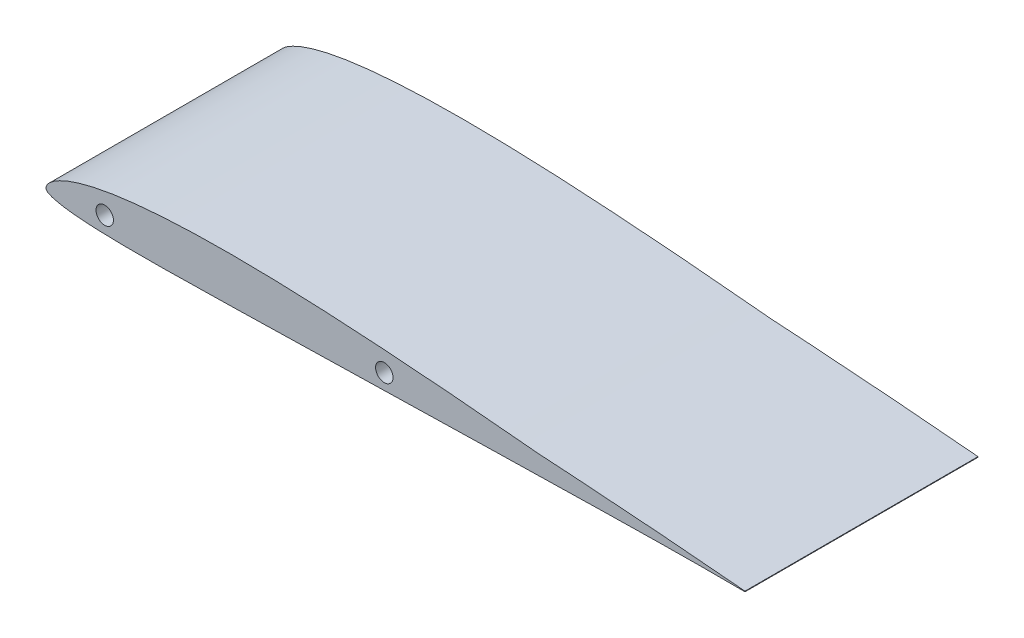
SolidWorks part; units mm, degrees
ref_plane "Front Plane" through (0, 0, 0) normal (0, 0, 1) x (1, 0, 0)
ref_plane "Top Plane" through (0, 0, 0) normal (0, 1, 0) x (1, 0, 0)
ref_plane "Right Plane" through (0, 0, 0) normal (1, 0, 0) x (0, 0, -1)
curve "Curve1"
  spline degree 3 poles (25.4, 0.0107, 0) (25.3506, 0.0152, 0) (25.2009, 0.0289, 0) (24.9376, 0.0531, 0) (24.6076, 0.082, 0) (24.2616, 0.1124, 0) (23.9125, 0.1431, 0) (23.5625, 0.1725, 0) (23.212, 0.2019, 0) (22.8613, 0.2307, 0) (22.5105, 0.2591, 0) (22.1596, 0.2869, 0) (21.8089, 0.314, 0) (21.4582, 0.3409, 0) (21.1077, 0.367, 0) (20.7573, 0.3928, 0) (20.407, 0.4182, 0) (20.0568, 0.4428, 0) (19.7068, 0.4673, 0) (19.3568, 0.4911, 0) (19.0069, 0.5145, 0) (18.6571, 0.5374, 0) (18.3335, 0.5583, 0) (18.0818, 0.5739, 0) (17.9246, 0.5843, 0) (17.8356, 0.5888, 0) (17.7472, 0.5983, 0) (17.5613, 0.6156, 0) (17.278, 0.6431, 0) (16.98, 0.6709, 0) (16.7137, 0.6956, 0) (16.4751, 0.7176, 0) (16.176, 0.7447, 0) (15.8267, 0.776, 0) (15.4701, 0.8073, 0) (15.1145, 0.838, 0) (14.7793, 0.8663, 0) (14.4495, 0.8936, 0) (14.1621, 0.9169, 0) (13.925, 0.9358, 0) (13.6642, 0.9563, 0) (13.3619, 0.9794, 0) (13.0103, 1.0056, 0) (12.659, 1.031, 0) (12.3077, 1.0554, 0) (11.9565, 1.0789, 0) (11.6054, 1.1014, 0) (11.2544, 1.1228, 0) (10.9034, 1.1432, 0) (10.5525, 1.1624, 0) (10.2016, 1.1803, 0) (9.8507, 1.197, 0) (9.5, 1.2123, 0) (9.1492, 1.2263, 0) (8.7986, 1.2386, 0) (8.448, 1.2494, 0) (8.0977, 1.2585, 0) (7.7474, 1.2658, 0) (7.3974, 1.2711, 0) (7.0475, 1.2745, 0) (6.6979, 1.2756, 0) (6.3485, 1.2744, 0) (5.9995, 1.2706, 0) (5.6509, 1.2642, 0) (5.3028, 1.2548, 0) (4.9554, 1.2422, 0) (4.6087, 1.2261, 0) (4.2629, 1.2062, 0) (3.9183, 1.1823, 0) (3.5751, 1.1536, 0) (3.2336, 1.12, 0) (2.8944, 1.0807, 0) (2.5581, 1.0351, 0) (2.2254, 0.9824, 0) (1.8975, 0.9214, 0) (1.5762, 0.8511, 0) (1.2643, 0.7698, 0) (0.9677, 0.6771, 0) (0.6972, 0.5737, 0) (0.4689, 0.4653, 0) (0.2948, 0.361, 0) (0.1747, 0.2696, 0) (0.0967, 0.1939, 0) (0.0471, 0.1311, 0) (0.0171, 0.0777, 0) (0.0019, 0.0319, 0) (-0.0016, -0.0085, 0) (0.0071, -0.0466, 0) (0.0322, -0.0832, 0) (0.0764, -0.1158, 0) (0.1405, -0.1489, 0) (0.2348, -0.1846, 0) (0.3747, -0.2244, 0) (0.5727, -0.265, 0) (0.8268, -0.3029, 0) (1.1218, -0.3343, 0) (1.4394, -0.3584, 0) (1.7684, -0.3763, 0) (2.1036, -0.389, 0) (2.4428, -0.3976, 0) (2.7846, -0.4031, 0) (3.1285, -0.4061, 0) (3.4739, -0.407, 0) (3.8205, -0.4061, 0) (4.168, -0.4035, 0) (4.5164, -0.3997, 0) (4.8654, -0.3948, 0) (5.2151, -0.389, 0) (5.5654, -0.3825, 0) (5.9165, -0.3755, 0) (6.2684, -0.368, 0) (6.621, -0.3604, 0) (6.9745, -0.3524, 0) (7.3287, -0.3442, 0) (7.6835, -0.336, 0) (8.039, -0.3276, 0) (8.3948, -0.3192, 0) (8.7511, -0.3108, 0) (9.1077, -0.3024, 0) (9.4646, -0.2939, 0) (9.8219, -0.2855, 0) (10.1795, -0.2771, 0) (10.5373, -0.2687, 0) (10.8952, -0.2603, 0) (11.2527, -0.252, 0) (11.6101, -0.2438, 0) (11.9672, -0.2355, 0) (12.3241, -0.2274, 0) (12.6807, -0.2193, 0) (13.0371, -0.2114, 0) (13.3934, -0.2033, 0) (13.6949, -0.1966, 0) (13.9592, -0.1908, 0) (14.1921, -0.1856, 0) (14.4749, -0.1792, 0) (14.7878, -0.1723, 0) (15.131, -0.1647, 0) (15.4754, -0.1569, 0) (15.8234, -0.1492, 0) (16.1349, -0.1423, 0) (16.4075, -0.1363, 0) (16.6379, -0.1313, 0) (16.9029, -0.1255, 0) (17.2072, -0.1189, 0) (17.4885, -0.1128, 0) (17.6791, -0.1088, 0) (17.7715, -0.1068, 0) (17.8501, -0.1053, 0) (18.0096, -0.1018, 0) (18.269, -0.0964, 0) (18.61, -0.0893, 0) (18.9621, -0.082, 0) (19.3141, -0.0749, 0) (19.666, -0.0678, 0) (20.0179, -0.0609, 0) (20.3698, -0.054, 0) (20.7219, -0.0473, 0) (21.074, -0.0408, 0) (21.4262, -0.0348, 0) (21.7784, -0.0292, 0) (22.1308, -0.0242, 0) (22.4832, -0.0197, 0) (22.8357, -0.0157, 0) (23.1883, -0.0125, 0) (23.5408, -0.0098, 0) (23.8935, -0.008, 0) (24.246, -0.0071, 0) (24.5963, -0.007, 0) (24.9308, -0.0084, 0) (25.198, -0.0096, 0) (25.3499, -0.0104, 0) (25.4, -0.0107, 0) knots 0 0 0 0 0.002901 0.008799 0.015478 0.022288 0.029131 0.035985 0.042847 0.049714 0.056581 0.063448 0.070313 0.077171 0.084031 0.090885 0.097737 0.104584 0.111432 0.118275 0.125116 0.131954 0.138793 0.144098 0.146709 0.148014 0.149313 0.151911 0.158945 0.165974 0.169425 0.174599 0.18 0.186998 0.195126 0.200949 0.20789 0.214818 0.220317 0.224762 0.228741 0.235631 0.242503 0.249376 0.256249 0.263115 0.269975 0.276837 0.283698 0.290553 0.297409 0.304262 0.311112 0.317958 0.324805 0.331647 0.338484 0.345319 0.352149 0.358974 0.365797 0.372613 0.37942 0.386225 0.393018 0.399801 0.406576 0.413331 0.420073 0.426793 0.433487 0.440154 0.446776 0.453353 0.459862 0.466294 0.472602 0.478718 0.484477 0.489534 0.493496 0.496331 0.498346 0.499841 0.500999 0.501915 0.502649 0.503345 0.504158 0.505185 0.506526 0.508376 0.511074 0.515031 0.520197 0.526109 0.532386 0.538838 0.545393 0.552019 0.558693 0.565404 0.572145 0.578909 0.585689 0.592488 0.599298 0.60612 0.612956 0.619809 0.626673 0.633554 0.640451 0.647364 0.654291 0.661227 0.668172 0.675126 0.682086 0.689049 0.69602 0.703 0.709987 0.71697 0.723948 0.73092 0.73789 0.744856 0.751814 0.758769 0.765721 0.77267 0.776424 0.78119 0.786305 0.792978 0.79951 0.806399 0.81314 0.819881 0.824633 0.829103 0.833367 0.840145 0.84692 0.849831 0.851305 0.852333 0.85443 0.860642 0.867519 0.87439 0.881257 0.888123 0.894989 0.901857 0.908727 0.915597 0.922469 0.929344 0.936217 0.943092 0.949972 0.956848 0.963729 0.970609 0.97749 0.984361 0.991109 0.997067 1 1 1 1
sketch "Sketch2" plane through (0, 0, 0) normal (0, 0, 1) x (1, 0, 0)
  line L0 (64.7182, -2.4991) -> (64.7182, -2.5635)
  spline S0 degree 3 poles (-239.8938, -3990.188) (87.2897, 0.8284) (55.8802, -2.7987) (24.9376, 0.0531) (24.6076, 0.082) (24.2616, 0.1124) (23.9125, 0.1431) (23.5625, 0.1725) (23.212, 0.2019) (22.8613, 0.2307) (22.5105, 0.2591) (22.1596, 0.2869) (21.8089, 0.314) (21.4582, 0.3409) (21.1077, 0.367) (20.7573, 0.3928) (20.407, 0.4182) (20.0568, 0.4428) (19.7068, 0.4673) (19.3568, 0.4911) (19.0069, 0.5145) (18.6571, 0.5374) (18.3335, 0.5583) (18.0818, 0.5739) (17.9246, 0.5843) (17.8356, 0.5888) (17.7472, 0.5983) (17.5613, 0.6156) (17.278, 0.6431) (16.98, 0.6709) (16.7137, 0.6956) (16.4751, 0.7176) (16.176, 0.7447) (15.8267, 0.776) (15.4701, 0.8073) (15.1145, 0.838) (14.7793, 0.8663) (14.4495, 0.8936) (14.1621, 0.9169) (13.925, 0.9358) (13.6642, 0.9563) (13.3619, 0.9794) (13.0103, 1.0056) (12.659, 1.031) (12.1907, 1.0635) (11.7225, 1.0942) (11.2544, 1.1228) (10.9034, 1.1432) (10.4356, 1.1688) (9.9677, 1.1919) (9.5, 1.2123) (9.1492, 1.2263) (8.7986, 1.2386) (8.448, 1.2494) (8.0977, 1.2585) (7.7474, 1.2658) (7.3974, 1.2711) (7.0475, 1.2745) (6.6979, 1.2756) (6.3485, 1.2744) (5.9995, 1.2706) (5.6509, 1.2642) (5.3028, 1.2548) (4.9554, 1.2422) (4.6087, 1.2261) (4.2629, 1.2062) (3.9183, 1.1823) (3.5751, 1.1536) (3.2336, 1.12) (2.8944, 1.0807) (2.5581, 1.0351) (2.2254, 0.9824) (1.8975, 0.9214) (1.5762, 0.8511) (1.2643, 0.7698) (0.9677, 0.6771) (0.6972, 0.5737) (0.4689, 0.4653) (0.2948, 0.361) (0.1747, 0.2696) (0.0967, 0.1939) (0.0471, 0.1311) (0.0171, 0.0777) (0.0019, 0.0319) (-0.0016, -0.0085) (0.0071, -0.0466) (0.0322, -0.0832) (0.0764, -0.1158) (0.1405, -0.1489) (0.2348, -0.1846) (0.3747, -0.2244) (0.5727, -0.265) (0.8268, -0.3029) (1.1218, -0.3343) (1.4394, -0.3584) (1.7684, -0.3763) (2.1036, -0.389) (2.4428, -0.3976) (2.7846, -0.4031) (3.1285, -0.4061) (3.4739, -0.407) (3.8205, -0.4061) (4.168, -0.4035) (4.5164, -0.3997) (4.8654, -0.3948) (5.2151, -0.389) (5.5654, -0.3825) (5.9165, -0.3755) (6.2684, -0.368) (6.621, -0.3604) (6.9745, -0.3524) (7.3287, -0.3442) (7.8022, -0.3332) (8.2764, -0.322) (8.7511, -0.3108) (9.1077, -0.3024) (9.4646, -0.2939) (9.8219, -0.2855) (10.1795, -0.2771) (10.5373, -0.2687) (10.8952, -0.2603) (11.2527, -0.252) (11.6101, -0.2438) (11.9672, -0.2355) (12.3241, -0.2274) (12.6807, -0.2193) (13.0371, -0.2114) (13.3934, -0.2033) (13.6949, -0.1966) (14.0466, -0.1889) (14.3934, -0.181) (14.7878, -0.1723) (15.131, -0.1647) (15.4754, -0.1569) (15.8234, -0.1492) (16.1349, -0.1423) (16.4075, -0.1363) (16.6379, -0.1313) (16.9029, -0.1255) (17.2072, -0.1189) (17.4885, -0.1128) (17.6791, -0.1088) (17.7715, -0.1068) (17.8501, -0.1053) (18.0096, -0.1018) (18.269, -0.0964) (18.61, -0.0893) (18.9621, -0.082) (19.3141, -0.0749) (19.666, -0.0678) (20.0179, -0.0609) (20.3698, -0.054) (20.7219, -0.0473) (21.074, -0.0408) (21.4262, -0.0348) (21.8959, -0.0274) (22.3658, -0.021) (22.8357, -0.0157) (23.1883, -0.0125) (23.5408, -0.0098) (23.8935, -0.008) (24.246, -0.0071) (24.5963, -0.007) (24.9308, -0.0084) (54.9827, -0.1451) (84.8865, -7.0769) (134.0951, 3997.4792) knots -1.803212 -1.803212 -1.803212 -1.803212 0.002901 0.008799 0.015478 0.022288 0.029131 0.035985 0.042847 0.049714 0.056581 0.063448 0.070313 0.077171 0.084031 0.090885 0.097737 0.104584 0.111432 0.118275 0.125116 0.131954 0.138793 0.144098 0.146709 0.148014 0.149313 0.151911 0.158945 0.165974 0.169425 0.174599 0.18 0.186998 0.195126 0.200949 0.20789 0.214818 0.220317 0.224762 0.228741 0.235631 0.242503 0.249376 0.256249 0.269975 0.276837 0.283698 0.290553 0.304262 0.311112 0.317958 0.324805 0.331647 0.338484 0.345319 0.352149 0.358974 0.365797 0.372613 0.37942 0.386225 0.393018 0.399801 0.406576 0.413331 0.420073 0.426793 0.433487 0.440154 0.446776 0.453353 0.459862 0.466294 0.472602 0.478718 0.484477 0.489534 0.493496 0.496331 0.498346 0.499841 0.500999 0.501915 0.502649 0.503345 0.504158 0.505185 0.506526 0.508376 0.511074 0.515031 0.520197 0.526109 0.532386 0.538838 0.545393 0.552019 0.558693 0.565404 0.572145 0.578909 0.585689 0.592488 0.599298 0.60612 0.612956 0.619809 0.626673 0.633554 0.640451 0.647364 0.654291 0.668172 0.675126 0.682086 0.689049 0.69602 0.703 0.709987 0.71697 0.723948 0.73092 0.73789 0.744856 0.751814 0.758769 0.765721 0.77267 0.776424 0.786305 0.792978 0.79951 0.806399 0.81314 0.819881 0.824633 0.829103 0.833367 0.840145 0.84692 0.849831 0.851305 0.852333 0.85443 0.860642 0.867519 0.87439 0.881257 0.888123 0.894989 0.901857 0.908727 0.915597 0.922469 0.929344 0.943092 0.949972 0.956848 0.963729 0.970609 0.97749 0.984361 0.991109 0.997067 2.743266 2.743266 2.743266 2.743266 only from (25.4, 0.0107) to (25.4, -0.0107) construction
  spline S1 degree 3 poles (25.4, 0.0107) (25.3506, 0.0152) (25.2009, 0.0289) (24.9376, 0.0531) (24.6076, 0.082) (24.2616, 0.1124) (23.9125, 0.1431) (23.5625, 0.1725) (23.212, 0.2019) (22.8613, 0.2307) (22.5105, 0.2591) (22.1596, 0.2869) (21.8089, 0.314) (21.4582, 0.3409) (21.1077, 0.367) (20.7573, 0.3928) (20.407, 0.4182) (20.0568, 0.4428) (19.7068, 0.4673) (19.3568, 0.4911) (19.0069, 0.5145) (18.6571, 0.5374) (18.3335, 0.5583) (18.0818, 0.5739) (17.9246, 0.5843) (17.8356, 0.5888) (17.7472, 0.5983) (17.5613, 0.6156) (17.278, 0.6431) (16.98, 0.6709) (16.7137, 0.6956) (16.4751, 0.7176) (16.176, 0.7447) (15.8267, 0.776) (15.4701, 0.8073) (15.1145, 0.838) (14.7793, 0.8663) (14.4495, 0.8936) (14.1621, 0.9169) (13.925, 0.9358) (13.6642, 0.9563) (13.3619, 0.9794) (13.0103, 1.0056) (12.659, 1.031) (12.1907, 1.0635) (11.7225, 1.0942) (11.2544, 1.1228) (10.9034, 1.1432) (10.4356, 1.1688) (9.9677, 1.1919) (9.5, 1.2123) (9.1492, 1.2263) (8.7986, 1.2386) (8.448, 1.2494) (8.0977, 1.2585) (7.7474, 1.2658) (7.3974, 1.2711) (7.0475, 1.2745) (6.6979, 1.2756) (6.3485, 1.2744) (5.9995, 1.2706) (5.6509, 1.2642) (5.3028, 1.2548) (4.9554, 1.2422) (4.6087, 1.2261) (4.2629, 1.2062) (3.9183, 1.1823) (3.5751, 1.1536) (3.2336, 1.12) (2.8944, 1.0807) (2.5581, 1.0351) (2.2254, 0.9824) (1.8975, 0.9214) (1.5762, 0.8511) (1.2643, 0.7698) (0.9677, 0.6771) (0.6972, 0.5737) (0.4689, 0.4653) (0.2948, 0.361) (0.1747, 0.2696) (0.0967, 0.1939) (0.0471, 0.1311) (0.0171, 0.0777) (0.0019, 0.0319) (-0.0016, -0.0085) (0.0071, -0.0466) (0.0322, -0.0832) (0.0764, -0.1158) (0.1405, -0.1489) (0.2348, -0.1846) (0.3747, -0.2244) (0.5727, -0.265) (0.8268, -0.3029) (1.1218, -0.3343) (1.4394, -0.3584) (1.7684, -0.3763) (2.1036, -0.389) (2.4428, -0.3976) (2.7846, -0.4031) (3.1285, -0.4061) (3.4739, -0.407) (3.8205, -0.4061) (4.168, -0.4035) (4.5164, -0.3997) (4.8654, -0.3948) (5.2151, -0.389) (5.5654, -0.3825) (5.9165, -0.3755) (6.2684, -0.368) (6.621, -0.3604) (6.9745, -0.3524) (7.3287, -0.3442) (7.8022, -0.3332) (8.2764, -0.322) (8.7511, -0.3108) (9.1077, -0.3024) (9.4646, -0.2939) (9.8219, -0.2855) (10.1795, -0.2771) (10.5373, -0.2687) (10.8952, -0.2603) (11.2527, -0.252) (11.6101, -0.2438) (11.9672, -0.2355) (12.3241, -0.2274) (12.6807, -0.2193) (13.0371, -0.2114) (13.3934, -0.2033) (13.6949, -0.1966) (14.0466, -0.1889) (14.3934, -0.181) (14.7878, -0.1723) (15.131, -0.1647) (15.4754, -0.1569) (15.8234, -0.1492) (16.1349, -0.1423) (16.4075, -0.1363) (16.6379, -0.1313) (16.9029, -0.1255) (17.2072, -0.1189) (17.4885, -0.1128) (17.6791, -0.1088) (17.7715, -0.1068) (17.8501, -0.1053) (18.0096, -0.1018) (18.269, -0.0964) (18.61, -0.0893) (18.9621, -0.082) (19.3141, -0.0749) (19.666, -0.0678) (20.0179, -0.0609) (20.3698, -0.054) (20.7219, -0.0473) (21.074, -0.0408) (21.4262, -0.0348) (21.8959, -0.0274) (22.3658, -0.021) (22.8357, -0.0157) (23.1883, -0.0125) (23.5408, -0.0098) (23.8935, -0.008) (24.246, -0.0071) (24.5963, -0.007) (24.9308, -0.0084) (25.198, -0.0096) (25.3499, -0.0104) (25.4, -0.0107) knots 0 0 0 0 0.002901 0.008799 0.015478 0.022288 0.029131 0.035985 0.042847 0.049714 0.056581 0.063448 0.070313 0.077171 0.084031 0.090885 0.097737 0.104584 0.111432 0.118275 0.125116 0.131954 0.138793 0.144098 0.146709 0.148014 0.149313 0.151911 0.158945 0.165974 0.169425 0.174599 0.18 0.186998 0.195126 0.200949 0.20789 0.214818 0.220317 0.224762 0.228741 0.235631 0.242503 0.249376 0.256249 0.269975 0.276837 0.283698 0.290553 0.304262 0.311112 0.317958 0.324805 0.331647 0.338484 0.345319 0.352149 0.358974 0.365797 0.372613 0.37942 0.386225 0.393018 0.399801 0.406576 0.413331 0.420073 0.426793 0.433487 0.440154 0.446776 0.453353 0.459862 0.466294 0.472602 0.478718 0.484477 0.489534 0.493496 0.496331 0.498346 0.499841 0.500999 0.501915 0.502649 0.503345 0.504158 0.505185 0.506526 0.508376 0.511074 0.515031 0.520197 0.526109 0.532386 0.538838 0.545393 0.552019 0.558693 0.565404 0.572145 0.578909 0.585689 0.592488 0.599298 0.60612 0.612956 0.619809 0.626673 0.633554 0.640451 0.647364 0.654291 0.668172 0.675126 0.682086 0.689049 0.69602 0.703 0.709987 0.71697 0.723948 0.73092 0.73789 0.744856 0.751814 0.758769 0.765721 0.77267 0.776424 0.786305 0.792978 0.79951 0.806399 0.81314 0.819881 0.824633 0.829103 0.833367 0.840145 0.84692 0.849831 0.851305 0.852333 0.85443 0.860642 0.867519 0.87439 0.881257 0.888123 0.894989 0.901857 0.908727 0.915597 0.922469 0.929344 0.943092 0.949972 0.956848 0.963729 0.970609 0.97749 0.984361 0.991109 0.997067 1 1 1 1
  spline S2 degree 3 poles (64.7182, -2.4991) (64.5701, -2.4856) (64.1209, -2.4447) (63.3309, -2.3719) (62.341, -2.2854) (61.3029, -2.194) (60.2557, -2.1021) (59.2056, -2.0138) (58.1543, -1.9255) (57.1021, -1.8393) (56.0496, -1.7541) (54.9971, -1.6706) (53.9448, -1.5894) (52.8928, -1.5086) (51.8413, -1.4302) (50.79, -1.3528) (49.7392, -1.2768) (48.6886, -1.2029) (47.6385, -1.1294) (46.5885, -1.058) (45.539, -0.9879) (44.4895, -0.919) (43.5186, -0.8563) (42.7637, -0.8095) (42.2921, -0.7784) (42.0251, -0.7648) (41.7599, -0.7364) (41.2021, -0.6846) (40.3521, -0.602) (39.4582, -0.5186) (38.6592, -0.4445) (37.9433, -0.3785) (37.0463, -0.2971) (35.9983, -0.2032) (34.9286, -0.1093) (33.8617, -0.0174) (32.8559, 0.0676) (31.8666, 0.1496) (31.0046, 0.2194) (30.2932, 0.276) (29.5106, 0.3376) (28.6039, 0.4069) (27.5492, 0.4855) (26.4951, 0.5616) (25.0904, 0.6593) (23.6858, 0.7513) (22.2814, 0.8372) (21.2285, 0.8983) (19.8249, 0.975) (18.4214, 1.0444) (17.018, 1.1057) (15.9659, 1.1476) (14.9139, 1.1846) (13.8623, 1.2169) (12.8111, 1.2441) (11.7605, 1.2661) (10.7104, 1.2821) (9.6608, 1.2923) (8.6118, 1.2956) (7.5637, 1.2919) (6.5167, 1.2806) (5.471, 1.2613) (4.4267, 1.2331) (3.3842, 1.1953) (2.3442, 1.1471) (1.3068, 1.0874) (0.273, 1.0155) (-0.7566, 0.9296) (-1.781, 0.8288) (-2.7985, 0.7107) (-3.8076, 0.574) (-4.8055, 0.4158) (-5.7892, 0.233) (-6.7532, 0.022) (-7.6888, -0.2218) (-8.5788, -0.5001) (-9.3901, -0.8102) (-10.0753, -1.1355) (-10.5975, -1.4483) (-10.9578, -1.7224) (-11.1917, -1.9495) (-11.3405, -2.1379) (-11.4306, -2.2981) (-11.4763, -2.4357) (-11.4868, -2.5569) (-11.4606, -2.6712) (-11.3854, -2.7809) (-11.2527, -2.8786) (-11.0604, -2.978) (-10.7776, -3.0852) (-10.3578, -3.2045) (-9.7638, -3.3263) (-9.0013, -3.4399) (-8.1166, -3.5341) (-7.1637, -3.6065) (-6.1766, -3.6602) (-5.171, -3.6983) (-4.1536, -3.7242) (-3.128, -3.7407) (-2.0964, -3.7496) (-1.0602, -3.7524) (-0.0205, -3.7495) (1.0223, -3.7419) (2.0673, -3.7305) (3.1144, -3.7156) (4.1634, -3.6983) (5.2145, -3.6788) (6.2678, -3.6579) (7.3234, -3.6353) (8.3812, -3.6124) (9.4415, -3.5884) (10.5042, -3.5639) (11.9247, -3.5309) (13.3473, -3.4972) (14.7715, -3.4636) (15.8413, -3.4384) (16.912, -3.413) (17.9837, -3.3879) (19.0566, -3.3625) (20.1302, -3.3374) (21.2036, -3.3123) (22.2763, -3.2874) (23.3484, -3.2628) (24.4198, -3.2379) (25.4905, -3.2136) (26.5604, -3.1893) (27.6295, -3.1654) (28.6983, -3.1413) (29.603, -3.1212) (30.6578, -3.0979) (31.6985, -3.0744) (32.8816, -3.0482) (33.9112, -3.0253) (34.9444, -3.0021) (35.9884, -2.979) (36.9227, -2.9583) (37.7408, -2.9402) (38.4319, -2.9252) (39.2268, -2.9078) (40.1399, -2.8881) (40.9835, -2.8698) (41.5555, -2.8578) (41.8328, -2.8517) (42.0685, -2.8472) (42.547, -2.8367) (43.3252, -2.8205) (44.3481, -2.7991) (45.4046, -2.7774) (46.4604, -2.7561) (47.516, -2.7348) (48.5718, -2.7141) (49.6277, -2.6933) (50.6838, -2.6733) (51.7401, -2.6536) (52.7967, -2.6358) (54.2058, -2.6134) (55.6154, -2.5943) (57.0252, -2.5783) (58.0829, -2.5687) (59.1407, -2.5606) (60.1987, -2.5553) (61.2563, -2.5526) (62.3071, -2.5522) (63.3105, -2.5564) (64.1121, -2.56) (64.5678, -2.5626) (64.7182, -2.5635) knots 0 0 0 0 0.002901 0.008799 0.015478 0.022288 0.029131 0.035985 0.042847 0.049714 0.056581 0.063448 0.070313 0.077171 0.084031 0.090885 0.097737 0.104584 0.111432 0.118275 0.125116 0.131954 0.138793 0.144098 0.146709 0.148014 0.149313 0.151911 0.158945 0.165974 0.169425 0.174599 0.18 0.186998 0.195126 0.200949 0.20789 0.214818 0.220317 0.224762 0.228741 0.235631 0.242503 0.249376 0.256249 0.269975 0.276837 0.283698 0.290553 0.304262 0.311112 0.317958 0.324805 0.331647 0.338484 0.345319 0.352149 0.358974 0.365797 0.372613 0.37942 0.386225 0.393018 0.399801 0.406576 0.413331 0.420073 0.426793 0.433487 0.440154 0.446776 0.453353 0.459862 0.466294 0.472602 0.478718 0.484477 0.489534 0.493496 0.496331 0.498346 0.499841 0.500999 0.501915 0.502649 0.503345 0.504158 0.505185 0.506526 0.508376 0.511074 0.515031 0.520197 0.526109 0.532386 0.538838 0.545393 0.552019 0.558693 0.565404 0.572145 0.578909 0.585689 0.592488 0.599298 0.60612 0.612956 0.619809 0.626673 0.633554 0.640451 0.647364 0.654291 0.668172 0.675126 0.682086 0.689049 0.69602 0.703 0.709987 0.71697 0.723948 0.73092 0.73789 0.744856 0.751814 0.758769 0.765721 0.77267 0.776424 0.786305 0.792978 0.79951 0.806399 0.81314 0.819881 0.824633 0.829103 0.833367 0.840145 0.84692 0.849831 0.851305 0.852333 0.85443 0.860642 0.867519 0.87439 0.881257 0.888123 0.894989 0.901857 0.908727 0.915597 0.922469 0.929344 0.943092 0.949972 0.956848 0.963729 0.970609 0.97749 0.984361 0.991109 0.997067 1 1 1 1
extrude "Boss-Extrude1" add sketch "Sketch2" along normal mid plane 25.4
sketch "Sketch3" plane through (0, 0, 12.7) normal (0, 0, 1) x (1, 0, 0)
  circle A0 centre (-5.08, -1.905) radius 0.9525
  circle A1 centre (25.4, -1.524) radius 0.9525
  dimension "D1" = 1.905
  dimension "D4" = 1.905
  dimension "D2" = 5.08
  dimension "D3" = 1.905
  dimension "D5" = 25.4
  dimension "D6" = 1.524
extrude "Cut-Extrude1" cut sketch "Sketch3" against normal through all
